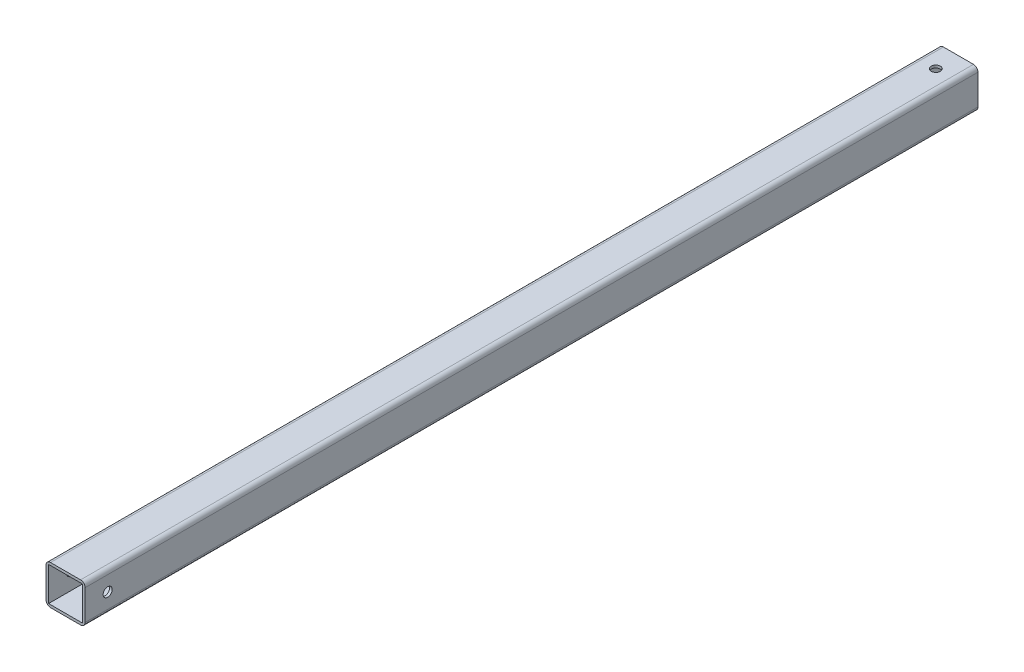
SolidWorks part; units mm, degrees
material "Hexcel AS4C (3000 Filaments)"
ref_plane "Front Plane" through (0, 0, 0) normal (0, 0, 1) x (1, 0, 0)
ref_plane "Top Plane" through (0, 0, 0) normal (0, 1, 0) x (1, 0, 0)
ref_plane "Right Plane" through (0, 0, 0) normal (1, 0, 0) x (0, 0, -1)
sketch "Sketch4" plane through (0, 0, 0) normal (0, 0, 1) x (1, 0, 0)
  line L1 (10.9855, -10.9855) -> (-10.9855, -10.9855)
  line L2 (10.9855, -10.9855) -> (10.9855, 10.9855)
  line L3 (10.9855, 10.9855) -> (-10.9855, 10.9855)
  line L4 (-10.9855, -10.9855) -> (-10.9855, 10.9855)
  line L5 (10.9855, -10.9855) -> (-10.9855, 10.9855) construction
  line L6 (10.9855, 10.9855) -> (-10.9855, -10.9855) construction
  line L7 (9.525, -9.525) -> (-9.525, -9.525)
  line L8 (9.525, -9.525) -> (9.525, 9.525)
  line L9 (9.525, 9.525) -> (-9.525, 9.525)
  line L10 (-9.525, -9.525) -> (-9.525, 9.525)
  line L11 (9.525, -9.525) -> (-9.525, 9.525) construction
  line L12 (9.525, 9.525) -> (-9.525, -9.525) construction
  point P0 (0, 0)
  point P1 (0, 0)
  dimension "D1" = 19.05
  dimension "D2" = 21.971
extrude "Boss-Extrude2" add sketch "Sketch4" along normal blind 501.65
fillet "Fillet1" radius 2.54 4 edges at (-10.9855, -10.9855, 250.825) (10.9855, -10.9855, 250.825) (-10.9855, 10.9855, 250.825) (10.9855, 10.9855, 250.825)
hole_wizard "#10 Clearance Hole1" positions "Sketch6" profile "Sketch7" hole size "#10" standard "ANSI Inch"
sketch "Sketch6" plane through (0, 10.9855, 0) normal (0, 1, 0) x (1, 0, 0)
  line L0 (8.4455, 0) -> (-8.4455, 0) construction
  point P0 (0, -12.7)
  point P6 (0, 0)
  dimension "D1" = 12.7
sketch "Sketch7" plane through (0, 10.9855, 12.7) normal (1, 0, 0) x (0, 0, 1)
  line L0 (0, 0) -> (0, 18.0438)
  line L1 (0, 18.0438) -> (2.5527, 16.51)
  line L2 (2.5527, 16.51) -> (2.5527, 0)
  line L5 (2.5527, 0) -> (0, 0)
  line L10 (0, 18.0438) -> (-2.5527, 16.51) construction
  line L11 (0, -6.35) -> (0, 107.95) construction
  dimension "Hole Dia." = 5.1054
  dimension "Hole Depth" = 16.51
  dimension "Drill Angle" = 118
hole_wizard "#10 Clearance Hole2" positions "Sketch8" profile "Sketch9" hole size "#10" standard "ANSI Inch" end condition through all
sketch "Sketch8" plane through (10.9855, 0, 0) normal (1, 0, 0) x (0, 0, -1)
  line L0 (-501.65, -8.4455) -> (-501.65, 8.4455) construction
  point P0 (-488.95, 0)
  dimension "D1" = 12.7
sketch "Sketch9" plane through (10.9855, 0, 488.95) normal (0, 1, 0) x (0, 0, -1)
  line L0 (0, 0) -> (0, 21.971)
  line L1 (0, 21.971) -> (2.5527, 21.971)
  line L2 (2.5527, 21.971) -> (2.5527, 0)
  line L5 (2.5527, 0) -> (0, 0)
  line L11 (0, -6.35) -> (0, 107.95) construction
  dimension "Thru Hole Dia." = 5.1054
  dimension "Thru Hole Depth" = 21.971
